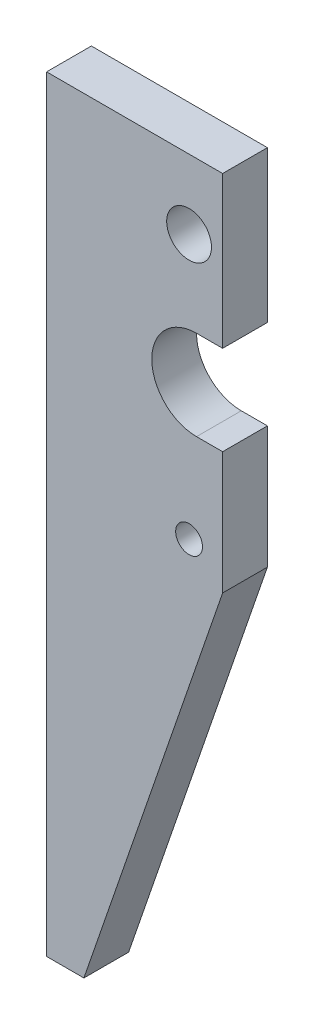
SolidWorks part; units mm, degrees
ref_plane "Plano frontal" through (0, 0, 0) normal (0, 0, 1) x (1, 0, 0)
ref_plane "Plano superior" through (0, 0, 0) normal (0, 1, 0) x (1, 0, 0)
ref_plane "Plano direito" through (0, 0, 0) normal (1, 0, 0) x (0, 0, -1)
sketch "Model" plane through (0, 0, 0) normal (0, 0, 1) x (1, 0, 0)
  line L0 (57.1737, 108.3696) -> (33.5737, 108.3696)
  line L1 (57.1737, 76.0713) -> (57.1737, 59.6713)
  line L2 (57.1737, 108.3696) -> (57.1737, 88.0713)
  line L3 (53.6737, 88.0713) -> (57.1737, 88.0713)
  line L4 (33.5737, 108.3696) -> (33.5737, 5.6713)
  line L5 (33.5737, 5.6713) -> (38.5737, 5.6713)
  line L6 (38.5737, 5.6713) -> (57.1737, 59.6713)
  line L7 (53.6737, 76.0713) -> (57.1737, 76.0713)
  circle A0 centre (52.6737, 63.6713) radius 1.8
  circle A1 centre (52.6737, 99.0589) radius 3
  arc A2 (53.6737, 88.0713) -> (53.6737, 76.0713) centre (53.6737, 82.0713) ccw
extrude "Ressalto-extrusão1" add sketch "Model" along normal blind 6
